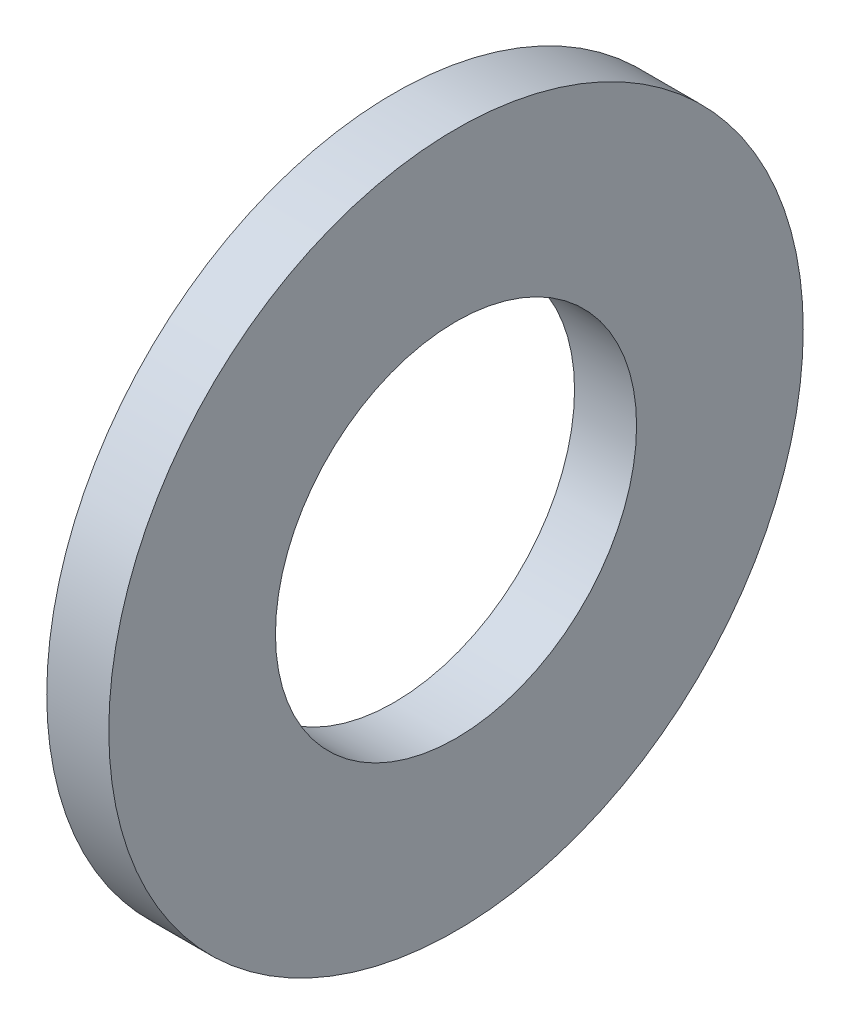
SolidWorks part; units mm, degrees
ref_plane "Front Plane" through (0, 0, 0) normal (0, 0, 1) x (1, 0, 0)
ref_plane "Top Plane" through (0, 0, 0) normal (0, 1, 0) x (1, 0, 0)
ref_plane "Right Plane" through (0, 0, 0) normal (1, 0, 0) x (0, 0, -1)
sketch "Sketch1" plane through (0, 0, 0) normal (1, 0, 0) x (0, 0, -1)
  circle A0 centre (0, 0) radius 9.525
  circle A1 centre (0, 0) radius 4.953
  dimension "OD" = 19.05
  dimension "ID" = 9.906
extrude "Boss-Extrude1" add sketch "Sketch1" along normal blind 1.7018
